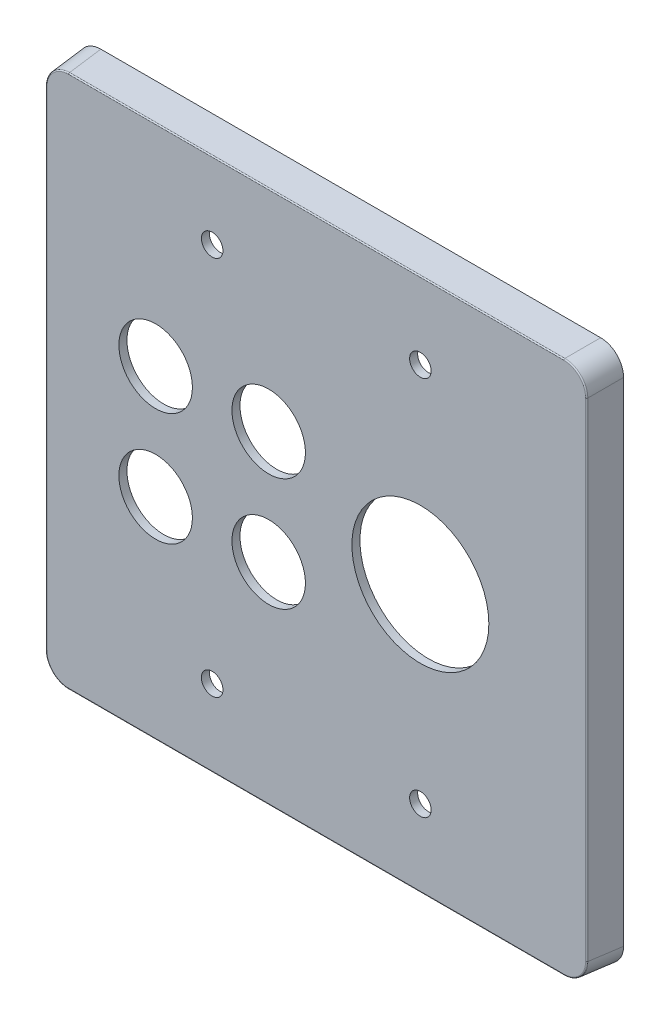
SolidWorks part; units mm, degrees
ref_plane "Front" through (0, 0, 0) normal (0, 0, 1) x (1, 0, 0)
ref_plane "Top" through (0, 0, 0) normal (0, 1, 0) x (1, 0, 0)
ref_plane "Right" through (0, 0, 0) normal (1, 0, 0) x (0, 0, -1)
sketch "Sketch1" plane through (0, 0, 0) normal (0, 0, 1) x (1, 0, 0)
  line L1 (60.325, -59.5312) -> (-60.325, -59.5313)
  line L2 (60.325, -59.5312) -> (60.325, 59.5312)
  line L3 (60.325, 59.5312) -> (-60.325, 59.5312)
  line L4 (-60.325, -59.5313) -> (-60.325, 59.5312)
  line L5 (60.325, -59.5312) -> (-60.325, 59.5312) construction
  line L6 (60.325, 59.5312) -> (-60.325, -59.5313) construction
  point P0 (0, 0)
  dimension "O'all Ht." = 119.0625
  dimension "O'all Wd." = 120.65
extrude "Boss-Extrude1" add sketch "Sketch1" along normal blind 7.62 draft 4
fillet "Fillet1" radius 5.08 4 edges at (-60.0586, -59.2648, 3.81) (60.0586, -59.2648, 3.81) (60.0586, 59.2648, 3.81) (-60.0586, 59.2648, 3.81)
fillet "Fillet2" radius 0.254 8 edges at (58.3094, 57.5156, 7.62) (59.7922, 0, 7.62) (58.3094, -57.5156, 7.62) (0, -58.9984, 7.62) (-58.3094, -57.5156, 7.62) (-59.7922, 0, 7.62) (-58.3094, 57.5156, 7.62) (0, 58.9984, 7.62)
shell "Shell1" thickness 1.778
sketch "Sketch2" plane through (0, 0, 7.62) normal (0, 0, 1) x (1, 0, 0)
  line L0 (-23.0188, 30.1625) -> (-23.0188, -30.1625) construction
  line L1 (-27.7813, -12.192) -> (-18.2563, -12.192)
  line L2 (-27.7813, -12.192) -> (-27.7813, 12.192)
  line L3 (-27.7813, 12.192) -> (-18.2563, 12.192)
  line L4 (-18.2563, -12.192) -> (-18.2563, 12.192)
  line L5 (-27.7813, -12.192) -> (-18.2563, 12.192) construction
  line L6 (-27.7813, 12.192) -> (-18.2563, -12.192) construction
  line L7 (0, 59.0149) -> (0, -59.0149) construction
  line L8 (-54.7411, 59.0149) -> (54.7411, 59.0149) construction
  line L9 (54.7411, -59.0149) -> (-54.7411, -59.0149) construction
  line L10 (27.7813, 12.192) -> (18.2563, -12.192) construction
  line L11 (27.7813, -12.192) -> (18.2563, 12.192) construction
  line L12 (23.0188, 30.1625) -> (23.0188, -30.1625) construction
  line L13 (18.2563, -12.192) -> (18.2563, 12.192)
  line L14 (27.7813, 12.192) -> (18.2563, 12.192)
  line L15 (27.7813, -12.192) -> (27.7813, 12.192)
  line L16 (27.7813, -12.192) -> (18.2563, -12.192)
  circle A0 centre (-23.0188, 30.1625) radius 2.3813
  circle A1 centre (-23.0188, -30.1625) radius 2.3813
  circle A2 centre (23.0188, -30.1625) radius 2.3813
  circle A3 centre (23.0188, 30.1625) radius 2.3813
  point P0 (-23.0188, 0)
  point P26 (23.0188, 0)
  dimension "D3" = 4.7625
  dimension "D1" = 9.525
  dimension "D2" = 24.384
  dimension "D4" = 60.325
  dimension "D5" = 46.0375
extrude "Single Toggle" [suppressed] cut sketch "Sketch2" against normal through all
sketch "Sketch3" plane through (0, 0, 7.62) normal (0, 0, 1) x (1, 0, 0)
  line L0 (-23.0187, 19.431) -> (-23.0188, -19.431) construction
  line L1 (-32.1654, 5.08) -> (-13.8721, 5.08)
  line L2 (-32.1654, 33.782) -> (-13.8721, 33.782)
  line L3 (-32.1654, -5.08) -> (-13.8721, -5.08)
  line L4 (-32.1654, -33.782) -> (-13.8721, -33.782)
  line L5 (0, 59.0149) -> (0, -59.0149) construction
  line L6 (-54.7411, 59.0149) -> (54.7411, 59.0149) construction
  line L7 (54.7411, -59.0149) -> (-54.7411, -59.0149) construction
  line L8 (23.0187, 19.431) -> (23.0187, -19.431) construction
  line L9 (32.1654, -33.782) -> (13.8721, -33.782)
  line L10 (32.1654, -5.08) -> (13.8721, -5.08)
  line L11 (32.1654, 33.782) -> (13.8721, 33.782)
  line L12 (32.1654, 5.08) -> (13.8721, 5.08)
  circle A0 centre (-23.0187, 19.431) radius 17.018 construction
  circle A1 centre (-23.0188, -19.431) radius 17.018 construction
  circle A2 centre (-23.0188, 0) radius 2.3813
  arc A3 (-32.1654, 33.782) -> (-32.1654, 5.08) centre (-23.0187, 19.431) ccw
  arc A4 (-13.8721, 33.782) -> (-13.8721, 5.08) centre (-23.0187, 19.431) cw
  arc A5 (-32.1654, -5.08) -> (-32.1654, -33.782) centre (-23.0188, -19.431) ccw
  arc A6 (-13.8721, -5.08) -> (-13.8721, -33.782) centre (-23.0188, -19.431) cw
  circle A7 centre (23.0187, -19.431) radius 17.018 construction
  circle A8 centre (23.0187, 19.431) radius 17.018 construction
  arc A9 (13.8721, -5.08) -> (13.8721, -33.782) centre (23.0187, -19.431) ccw
  arc A10 (32.1654, -5.08) -> (32.1654, -33.782) centre (23.0187, -19.431) cw
  arc A11 (13.8721, 33.782) -> (13.8721, 5.08) centre (23.0187, 19.431) ccw
  arc A12 (32.1654, 33.782) -> (32.1654, 5.08) centre (23.0187, 19.431) cw
  circle A13 centre (23.0188, 0) radius 2.3813
  dimension "D1" = 4.7625
  dimension "D2" = 34.036
  dimension "D3" = 38.862
  dimension "D4" = 67.564
  dimension "D5" = 46.0375
extrude "Outlet Cover" [suppressed] cut sketch "Sketch3" against normal through all
sketch "Sketch4" plane through (0, 0, 7.62) normal (0, 0, 1) x (1, 0, 0)
  line L0 (-23.0188, 48.4124) -> (-23.0188, -48.4124) construction
  line L1 (-39.6558, -33.401) -> (-6.3818, -33.401)
  line L2 (-39.6558, -33.401) -> (-39.6558, 33.401)
  line L3 (-39.6558, 33.401) -> (-6.3818, 33.401)
  line L4 (-6.3818, -33.401) -> (-6.3818, 33.401)
  line L5 (-39.6558, -33.401) -> (-6.3818, 33.401) construction
  line L6 (-39.6558, 33.401) -> (-6.3818, -33.401) construction
  line L7 (0, 59.0149) -> (0, -59.0149) construction
  line L8 (-54.7411, 59.0149) -> (54.7411, 59.0149) construction
  line L9 (54.7411, -59.0149) -> (-54.7411, -59.0149) construction
  line L10 (39.6558, 33.401) -> (6.3818, -33.401) construction
  line L11 (39.6558, -33.401) -> (6.3818, 33.401) construction
  line L12 (23.0188, 48.4124) -> (23.0188, -48.4124) construction
  line L13 (6.3818, -33.401) -> (6.3818, 33.401)
  line L14 (39.6558, 33.401) -> (6.3818, 33.401)
  line L15 (39.6558, -33.401) -> (39.6558, 33.401)
  line L16 (39.6558, -33.401) -> (6.3818, -33.401)
  circle A0 centre (-23.0188, 48.4124) radius 2.3812
  circle A1 centre (-23.0188, -48.4124) radius 2.3812
  circle A2 centre (23.0188, -48.4124) radius 2.3812
  circle A3 centre (23.0188, 48.4124) radius 2.3812
  point P0 (0, 0)
  point P10 (-23.0188, 0)
  point P25 (23.0188, 0)
  dimension "D1" = 4.7625
  dimension "D2" = 33.274
  dimension "D3" = 66.802
  dimension "D4" = 96.8248
  dimension "D5" = 46.0375
extrude "Rectangular Outlet" [suppressed] cut sketch "Sketch4" against normal through all
sketch "Sketch5" plane through (0, 0, 7.62) normal (0, 0, 1) x (1, 0, 0)
  line L0 (-23.0188, 42.037) -> (-23.0188, -42.037) construction
  line L1 (0, 59.5312) -> (0, -59.0149) construction
  line L2 (55.2574, 59.5312) -> (-55.2574, 59.5312) construction
  line L3 (54.7411, -59.0149) -> (-54.7411, -59.0149) construction
  line L4 (-23.0188, 0) -> (0, 0) construction
  line L5 (23.0188, 42.037) -> (23.0188, -42.037) construction
  circle A0 centre (-23.0188, 42.037) radius 2.3812
  circle A1 centre (-23.0188, -42.037) radius 2.3812
  circle A2 centre (23.0188, -42.037) radius 2.3812
  circle A3 centre (23.0188, 42.037) radius 2.3812
  point P18 (23.0188, 0)
  dimension "D1" = 4.7625
  dimension "D2" = 84.074
  dimension "D3" = 46.0375
extrude "Cut-Extrude1" cut sketch "Sketch5" against normal through all
sketch "Sketch6" plane through (0, 0, 7.62) normal (0, 0, 1) x (1, 0, 0)
  line L0 (-23.0188, 42.037) -> (-23.0188, -42.037) construction
  line L1 (23.0188, 42.037) -> (23.0188, -42.037) construction
  line L2 (-23.0188, 0) -> (23.0188, 0) construction
  line L3 (0, 0) -> (0, 58.7615) construction
  line L4 (54.7411, 58.7615) -> (-54.7411, 58.7615) construction
  line L5 (0, 0) -> (0, -58.7615) construction
  line L6 (-54.7411, -58.7615) -> (54.7411, -58.7615) construction
  circle A0 centre (23.0188, 0) radius 15.1397
  circle A1 centre (-35.5156, 12.4968) radius 8.128
  circle A2 centre (-10.522, 12.4968) radius 8.128
  circle A3 centre (-10.522, -12.4968) radius 8.128
  circle A4 centre (-35.5156, -12.4968) radius 8.128
  dimension "D1" = 30.2793
  dimension "D2" = 16.256
  dimension "D5" = 12.4968
  dimension "D6" = 12.4968
  dimension "D7" = 12.4968
  dimension "D3" = 12.4968
  dimension "D4" = 12.4968
  dimension "D8" = 12.4968
  dimension "D9" = 12.4968
  dimension "D10" = 12.4968
extrude "Cut-Extrude2" cut sketch "Sketch6" against normal through all
